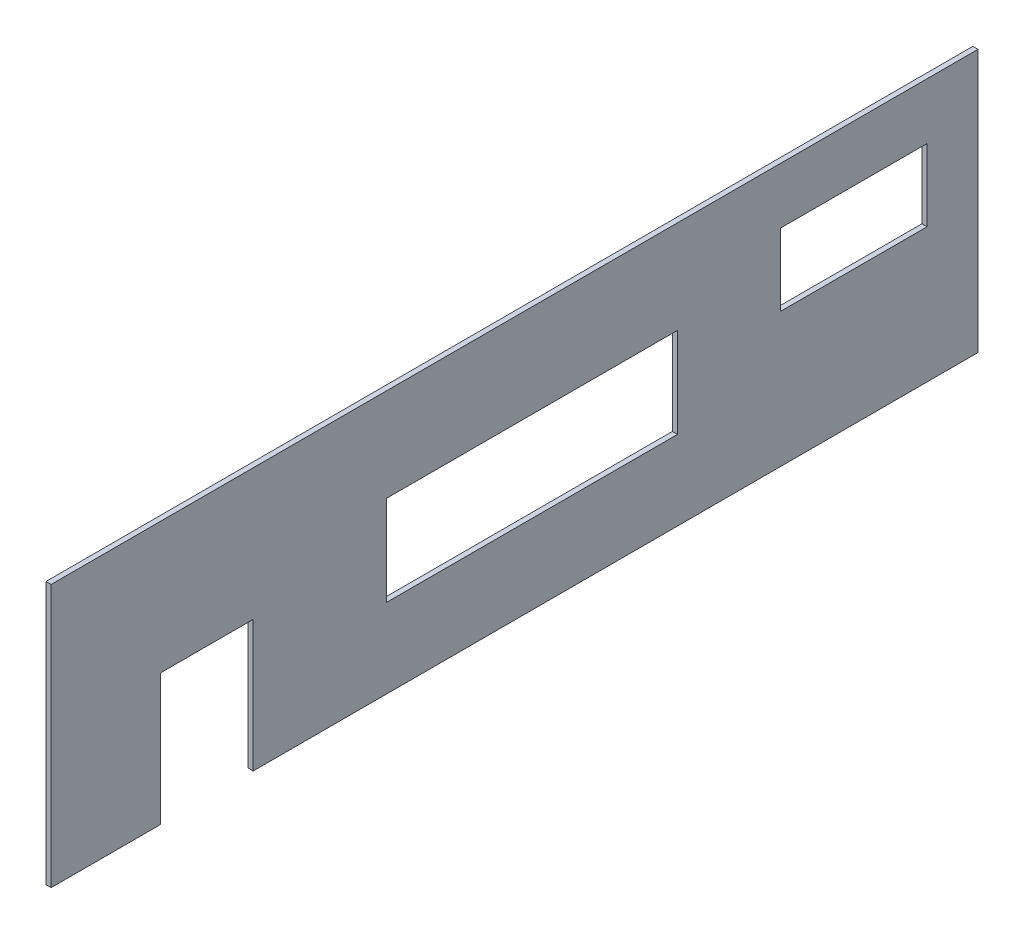
SolidWorks part; units mm, degrees
ref_plane "Front Plane" through (0, 0, 0) normal (0, 0, 1) x (1, 0, 0)
ref_plane "Top Plane" through (0, 0, 0) normal (0, 1, 0) x (1, 0, 0)
ref_plane "Right Plane" through (0, 0, 0) normal (1, 0, 0) x (0, 0, -1)
sketch "Sketch1" plane through (0, 0, 0) normal (1, 0, 0) x (0, 0, -1)
  line L1 (-117.3913, 121.3043) -> (242.6087, 121.3043)
  line L2 (-117.3913, 121.3043) -> (-117.3913, 19.3043)
  line L3 (-117.3913, 19.3043) -> (242.6087, 19.3043)
  line L4 (242.6087, 121.3043) -> (242.6087, 19.3043)
  dimension "D1" = 360
  dimension "D2" = 102
extrude "Boss-Extrude1" add sketch "Sketch1" along normal blind 2
sketch "Sketch2" plane through (0, 0, 0) normal (-1, 0, 0) x (0, 0, 1)
  line L0 (117.3913, 19.3043) -> (-242.6087, 19.3043) construction
  line L1 (74.9143, 19.3043) -> (38.9143, 19.3043)
  line L2 (74.9143, 19.3043) -> (74.9143, 70.3043)
  line L3 (74.9143, 70.3043) -> (38.9143, 70.3043)
  line L4 (38.9143, 19.3043) -> (38.9143, 70.3043)
  line L6 (-125.8663, 85.1308) -> (-12.8663, 85.1308)
  line L7 (-125.8663, 85.1308) -> (-125.8663, 50.1308)
  line L8 (-125.8663, 50.1308) -> (-12.8663, 50.1308)
  line L9 (-12.8663, 85.1308) -> (-12.8663, 50.1308)
  dimension "D1" = 113
  dimension "D2" = 35
  dimension "D3" = 36
  dimension "D4" = 51
extrude "Cut-Extrude1" cut sketch "Sketch2" against normal blind 10
sketch "Sketch3" plane through (0, 0, 0) normal (-1, 0, 0) x (0, 0, 1)
  line L1 (-222.8338, 99.5108) -> (-165.8338, 99.5108)
  line L2 (-222.8338, 99.5108) -> (-222.8338, 71.5108)
  line L3 (-222.8338, 71.5108) -> (-165.8338, 71.5108)
  line L4 (-165.8338, 99.5108) -> (-165.8338, 71.5108)
  dimension "D1" = 57
  dimension "D2" = 28
extrude "Cut-Extrude2" cut sketch "Sketch3" against normal blind 10
